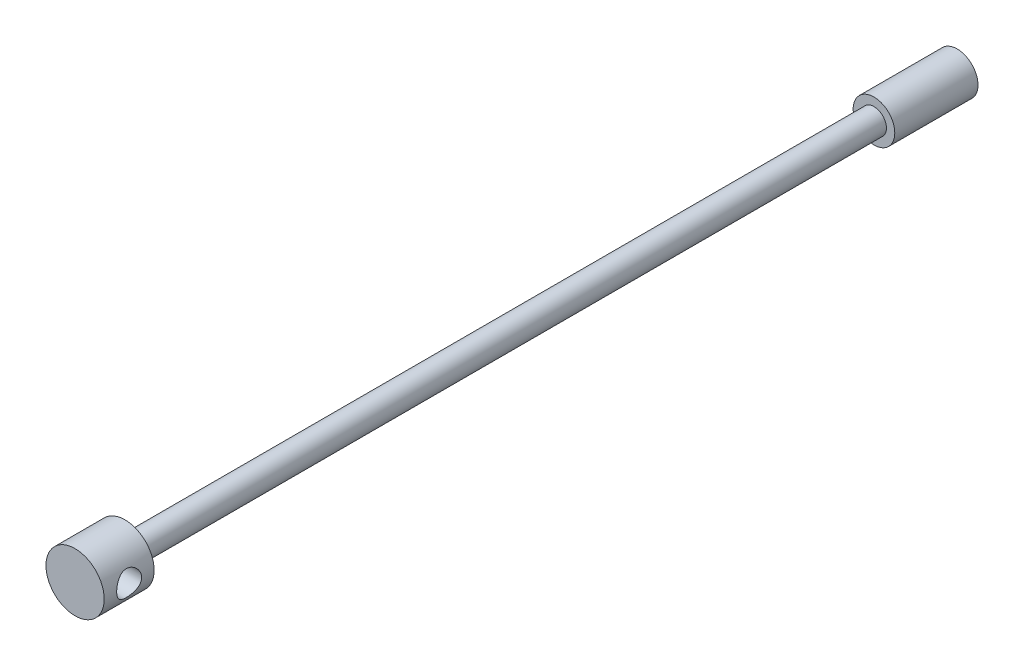
SolidWorks part; units mm, degrees
ref_plane "Ön Düzlem" through (0, 0, 0) normal (0, 0, 1) x (1, 0, 0)
ref_plane "Üst Düzlem" through (0, 0, 0) normal (0, 1, 0) x (1, 0, 0)
ref_plane "Sağ Düzlem" through (0, 0, 0) normal (1, 0, 0) x (0, 0, -1)
sketch "Çizim1" plane through (0, 0, 0) normal (0, 0, 1) x (1, 0, 0)
  circle A0 centre (0, 0) radius 1.25
  dimension "D1" = 2.5
extrude "Yükseklik-Ekstrüzyon1" add sketch "Çizim1" along normal blind 50
sketch "Çizim2" plane through (0, 0, 50) normal (0, 0, 1) x (1, 0, 0)
  circle A0 centre (0, 0) radius 0.75
  circle A1 centre (0, 0) radius 1.25 construction
  circle A2 centre (0, 0) radius 1.25
  dimension "D1" = 1.5
extrude "Kes-Ekstrüzyon1" cut sketch "Çizim2" against normal blind 45
sketch "Çizim3" plane through (0, 0, 50) normal (0, 0, 1) x (1, 0, 0)
  circle A0 centre (0, 0) radius 1.75
  dimension "D1" = 3.5
extrude "Yükseklik-Ekstrüzyon2" add sketch "Çizim3" along normal blind 3
ref_plane "Düzlem1" through (1.75, 0, 0) normal (1, 0, 0) x (0, 0, -1)
sketch "Çizim4" plane through (1.75, 0, 0) normal (1, 0, 0) x (0, 0, -1)
  line L0 (-50, -0.75) -> (-50, 0.75) construction
  line L1 (-53, -1.75) -> (-50, -1.75) construction
  circle A0 centre (-51.5, 0) radius 0.75
  dimension "D1" = 1.5
  dimension "D2" = 1.5
  dimension "D3" = 1.75
extrude "Kes-Ekstrüzyon2" cut sketch "Çizim4" against normal through all
